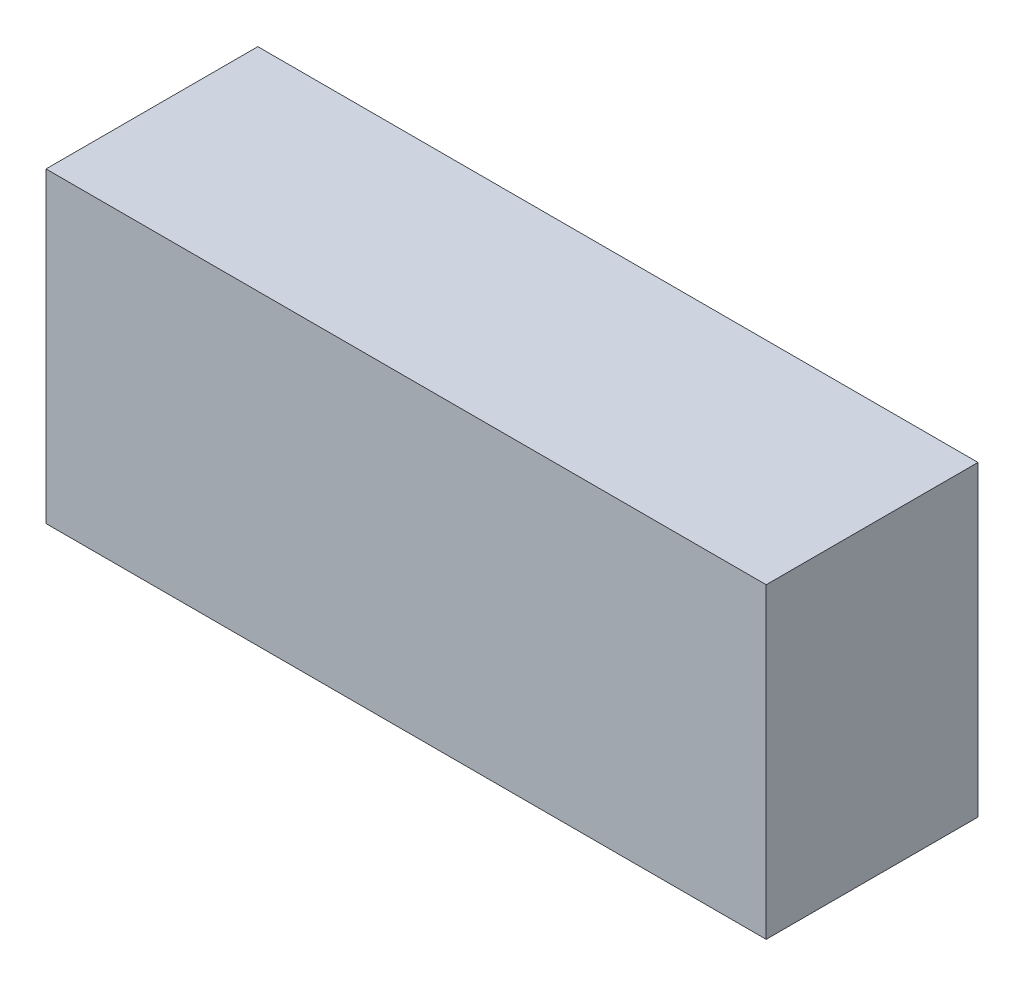
SolidWorks part; units mm, degrees
ref_plane "Alzado" through (0, 0, 0) normal (0, 0, 1) x (1, 0, 0)
ref_plane "Planta" through (0, 0, 0) normal (0, 1, 0) x (1, 0, 0)
ref_plane "Vista lateral" through (0, 0, 0) normal (1, 0, 0) x (0, 0, -1)
sketch "Croquis1" plane through (0, 0, 0) normal (0, 0, 1) x (1, 0, 0)
  line L1 (-38.3501, 29.9527) -> (29.6499, 29.9527)
  line L2 (-38.3501, 29.9527) -> (-38.3501, 0.9527)
  line L3 (-38.3501, 0.9527) -> (29.6499, 0.9527)
  line L4 (29.6499, 29.9527) -> (29.6499, 0.9527)
  dimension "D1" = 29
  dimension "D2" = 68
extrude "Saliente-Extruir1" add sketch "Croquis1" along normal blind 20
